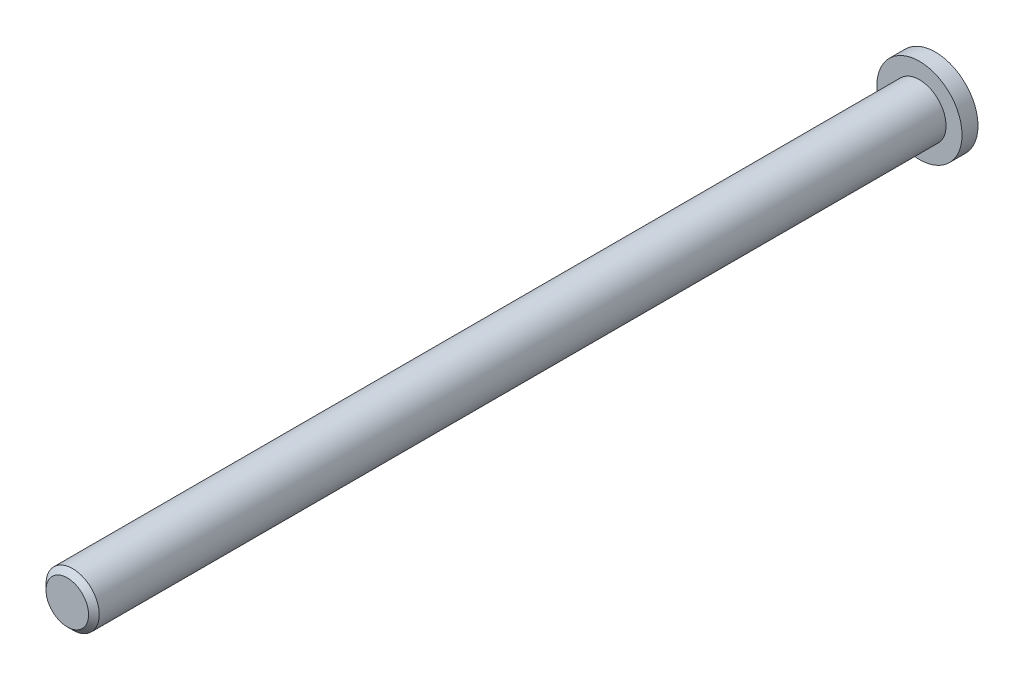
SolidWorks part; units mm, degrees
ref_plane "Front Plane" through (0, 0, 0) normal (0, 0, 1) x (1, 0, 0)
ref_plane "Top Plane" through (0, 0, 0) normal (0, 1, 0) x (1, 0, 0)
ref_plane "Right Plane" through (0, 0, 0) normal (1, 0, 0) x (0, 0, -1)
sketch "Sketch1" plane through (0, 0, 0) normal (0, 0, 1) x (1, 0, 0)
  circle A0 centre (0, 0) radius 4
  dimension "D1" = 8
extrude "Boss-Extrude1" add sketch "Sketch1" along normal blind 1.5
sketch "Sketch2" plane through (0, 0, 1.5) normal (0, 0, 1) x (1, 0, 0)
  circle A0 centre (0, 0) radius 2.5
  dimension "D1" = 5
extrude "Boss-Extrude2" add sketch "Sketch2" along normal blind 80
chamfer "Chamfer1" distance 0.5 angle 45 1 edges at (2.5, 0, 81.5)
